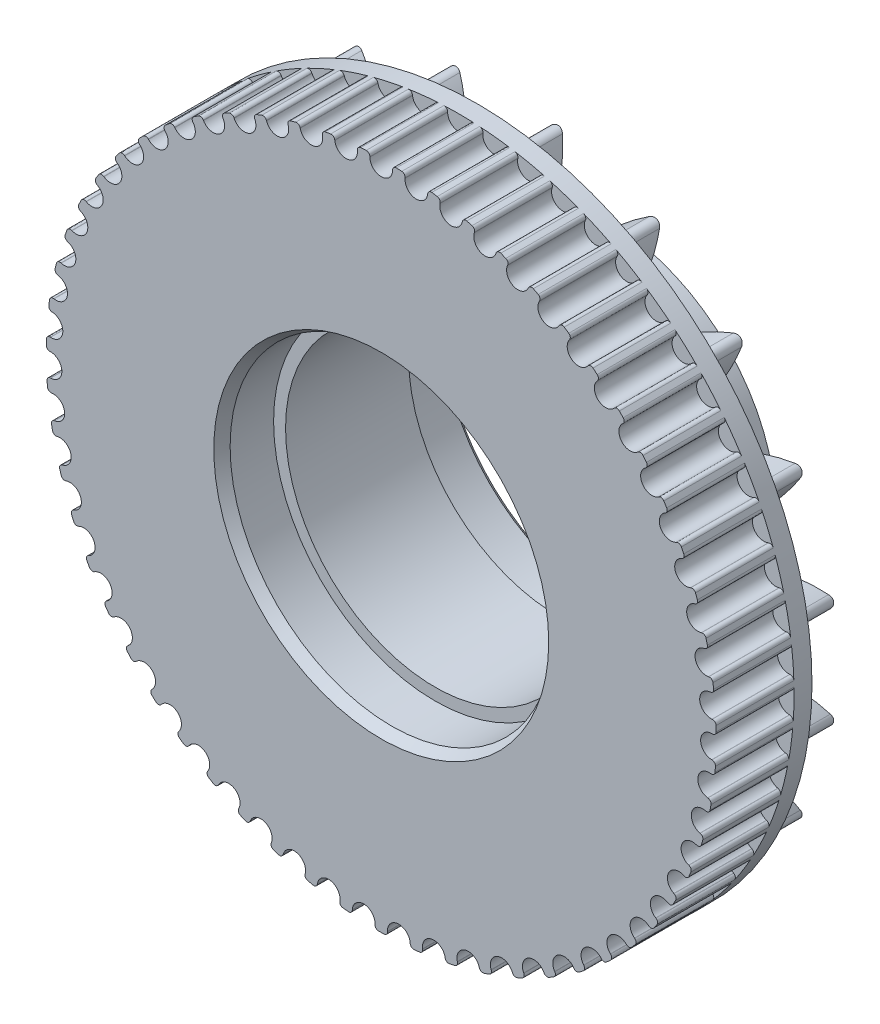
SolidWorks part; units mm, degrees
ref_plane "Ebene vorne" through (0, 0, 0) normal (0, 0, 1) x (1, 0, 0)
ref_plane "Ebene oben" through (0, 0, 0) normal (0, 1, 0) x (1, 0, 0)
ref_plane "Ebene rechts" through (0, 0, 0) normal (1, 0, 0) x (0, 0, -1)
ref_axis "Achse1" through (0, 0, 10.5) along (0, 0, -1)
sketch "Skizze1" plane through (0, 0, 0) normal (0, 1, 0) x (1, 0, 0)
  line L8 (-22.6426, 0) -> (-28.0075, 0)
  line L9 (-28.0075, 0) -> (-28.0075, 2.6824)
  line L20 (-22.6426, 0) -> (0, 0) construction
  line L21 (-28.0075, 2.6824) -> (-22.6426, 0)
  line L22 (-21.9953, 13.0928) -> (-28.0075, 2.6824) construction
  line L23 (-17.7821, 10.9861) -> (-21.9953, 13.0928) construction
  line L24 (0, 10.9861) -> (-17.7821, 10.9861) construction
  line L25 (0, 0) -> (0, 10.9861) construction
revolve "Rotation1" add sketch "Skizze1" angle 360 about L25
ref_plane "Ebene2" through (0, 4.5285, 9.0571) normal (0, 0.4472, 0.8944) x (1, 0, 0)
sketch "Skizze3" plane through (0, 4.5285, 9.0571) normal (0, 0.4472, 0.8944) x (1, 0, 0)
  arc A18 (-1.4236, 21.1116) -> (-4.8611, 26.4062) centre (-11.1009, 18.5919) ccw
  arc A19 (-1.4236, 21.1116) -> (-0.9483, 20.7597) centre (-0.9678, 21.2303) ccw
  arc A20 (0.9483, 20.7597) -> (-0.9483, 20.7597) centre (0, -2.1122) ccw
  arc A21 (0.9483, 20.7597) -> (1.4236, 21.1116) centre (0.9678, 21.2303) ccw
  arc A22 (4.8611, 26.4062) -> (1.4236, 21.1116) centre (11.1009, 18.5919) ccw
  arc A23 (4.8611, 26.4062) -> (-4.8611, 26.4062) centre (0, -2.1122) ccw
sketch "Skizze4" plane through (0, 0, 0) normal (1, 0, 0) x (0, 0, -1)
  line L1 (1.1824, 23.6426) -> (-4.8176, 23.6426)
  line L4 (2.6824, 28.0075) -> (2.6824, -28.0075) construction
  dimension "D1" = 1
  dimension "D2" = 6
  dimension "D3" = 1.5
sweep "Schnitt-Austragung1" [suppressed] cut profiles "Skizze3" path "Skizze4"
pattern_circular "Kreismuster1" [suppressed] count 20 over 360
sketch "Skizze12" plane through (0, 4.5285, 9.0571) normal (0, 0.4472, 0.8944) x (1, 0, 0)
  arc A12 (-1.5204, 21.0864) -> (-5.1003, 26.466) centre (-11.1009, 18.5919) ccw
  arc A13 (5.1003, 26.466) -> (-5.1003, 26.466) centre (0, -2.1122) ccw
  arc A14 (5.1003, 26.466) -> (1.5204, 21.0864) centre (11.1009, 18.5919) ccw
  arc A15 (0.9441, 20.6597) -> (1.5204, 21.0864) centre (0.9678, 21.2303) ccw
  arc A16 (0.9441, 20.6597) -> (-0.9441, 20.6597) centre (0, -2.1122) ccw
  arc A17 (-1.5204, 21.0864) -> (-0.9441, 20.6597) centre (-0.9678, 21.2303) ccw
  arc A18 (-1.5204, 21.0864) -> (-5.1003, 26.466) centre (-11.1009, 18.5919) ccw
  arc A19 (5.1003, 26.466) -> (-5.1003, 26.466) centre (0, -2.1122) ccw
  arc A20 (5.1003, 26.466) -> (1.5204, 21.0864) centre (11.1009, 18.5919) ccw
  arc A21 (0.9441, 20.6597) -> (1.5204, 21.0864) centre (0.9678, 21.2303) ccw
  arc A22 (0.9441, 20.6597) -> (-0.9441, 20.6597) centre (0, -2.1122) ccw
  arc A23 (-1.5204, 21.0864) -> (-0.9441, 20.6597) centre (-0.9678, 21.2303) ccw
  dimension "D1" = 0.1
sketch "Skizze13" plane through (0, 0, 0) normal (1, 0, 0) x (0, 0, -1)
  line L0 (1.1824, 23.6426) -> (-4.8176, 23.6426) construction
  line L1 (1.1824, 23.6426) -> (-4.8176, 23.6426)
sweep "Schnitt-Austragung3" cut profiles "Skizze12" path "Skizze13"
pattern_circular "Kreismuster5" count 20 over 360 about axis through (0, 0, 10.5) along (0, 0, -1) of "Schnitt-Austragung3"
fillet "Verrundung2" radius 0.6 20 edges at (12.7139, 24.9524, -1.3405) (4.3809, 27.66, -1.3405) (-4.3809, 27.66, -1.3405) (19.8024, 19.8024, -1.3405) (24.9524, 12.7139, -1.3405) (27.66, 4.3809, -1.3405) (27.66, -4.3809, -1.3405) (24.9524, -12.7139, -1.3405) (19.8024, -19.8024, -1.3405) (12.7139, -24.9524, -1.3405) (4.3809, -27.66, -1.3405) (-4.3809, -27.66, -1.3405) (-12.7139, -24.9524, -1.3405) (-19.8024, -19.8024, -1.3405) (-24.9524, -12.7139, -1.3405) (-27.66, -4.3809, -1.3405) (-27.66, 4.3809, -1.3405) (-24.9524, 12.7139, -1.3405) (-19.8024, 19.8024, -1.3405) (-12.7139, 24.9524, -1.3405)
sketch "Skizze5" plane through (0, 0, 0) normal (0, 0, 1) x (1, 0, 0)
  circle A1 centre (0, 0) radius 28.0075
  dimension "D1" = 56.015
extrude "Aufsatz-Linear austragen1" add sketch "Skizze5" along normal blind 8
sketch "Skizze8" plane through (0, 0, 8) normal (0, 0, 1) x (1, 0, 0)
  line L0 (0, 0) -> (0, 28.0075) construction
  line L1 (-0.95, 27.6575) -> (-0.95, 27.9914)
  line L2 (0.95, 27.6575) -> (0.95, 27.9914)
  circle A3 centre (0, 0) radius 28.0075 construction
  arc A4 (-0.95, 27.6575) -> (0.95, 27.6575) centre (0, 27.6575) ccw
  arc A5 (0.95, 27.9914) -> (-0.95, 27.9914) centre (0, 0) ccw
  dimension "D1" = 1.9
  dimension "D2" = 1.3
extrude "Schnitt-Linear austragen3" cut sketch "Skizze8" against normal blind 6.5 contours A5 L1 A4 L2
fillet "Verrundung1" radius 0.3 2 edges at (-0.95, 27.9914, 4.75) (0.95, 27.9914, 4.75)
pattern_circular "Kreismuster4" count 59 over 360 about axis through (0, 0, 0) along (0, 0, 1) of "Schnitt-Linear austragen3", "Verrundung1"
sketch "Skizze9" plane through (0, 0, 8) normal (0, 0, 1) x (1, 0, 0)
  circle A0 centre (0, 0) radius 12.5
  dimension "D1" = 25
extrude "Schnitt-Linear austragen4" cut sketch "Skizze9" against normal through all
sketch "Skizze10" plane through (0, 0, 0) normal (0, 0, -1) x (-1, 0, 0)
  circle A0 centre (0, 0) radius 14
  circle A1 centre (0, 0) radius 13.5
  dimension "D1" = 28
  dimension "D2" = 27
extrude "Aufsatz-Linear austragen2" add sketch "Skizze10" along normal up to surface (10.9861 mm away)
sketch "Skizze11" plane through (0, 0, 0) normal (0, 0, -1) x (-1, 0, 0)
  circle A0 centre (0, 0) radius 12.5
  circle A1 centre (0, 0) radius 13.5 construction
  circle A2 centre (0, 0) radius 13.5
  dimension "D1" = 25
extrude "Aufsatz-Linear austragen4" add sketch "Skizze11" along normal offset from surface (6.7861 mm away) 4.2
chamfer "Fase1" distance 0.4 angle 45 1 edges at (13.5, 0, -10.9861)
sketch "Skizze14" plane through (0, 0, 8) normal (0, 0, 1) x (1, 0, 0)
  circle A1 centre (0, 0) radius 13.5
  circle A2 centre (0, 0) radius 13.5
  dimension "D1" = 0
extrude "Schnitt-Linear austragen5" cut sketch "Skizze14" against normal blind 4.5
chamfer "Fase2" distance 0.5 angle 60 1 edges at (13.5, 0, 8)
